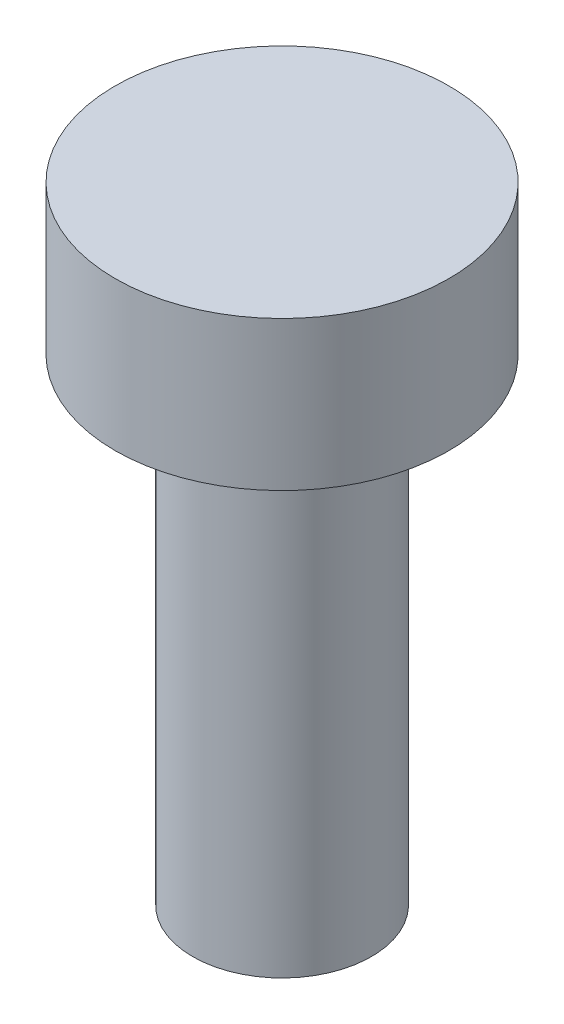
SolidWorks part; units mm, degrees
ref_plane "Front Plane" through (0, 0, 0) normal (0, 0, 1) x (1, 0, 0)
ref_plane "Top Plane" through (0, 0, 0) normal (0, 1, 0) x (1, 0, 0)
ref_plane "Right Plane" through (0, 0, 0) normal (1, 0, 0) x (0, 0, -1)
sketch "Sketch1" plane through (0, 0, 0) normal (0, 1, 0) x (1, 0, 0)
  circle A0 centre (0, 0) radius 1.5
  dimension "D1" = 3
extrude "Boss-Extrude1" add sketch "Sketch1" along normal blind 8
sketch "Sketch2" plane through (0, 8, 0) normal (0, 1, 0) x (1, 0, 0)
  circle A0 centre (0, 0) radius 2.8
  dimension "D1" = 5.6
extrude "Boss-Extrude2" add sketch "Sketch2" along normal blind 2.5
